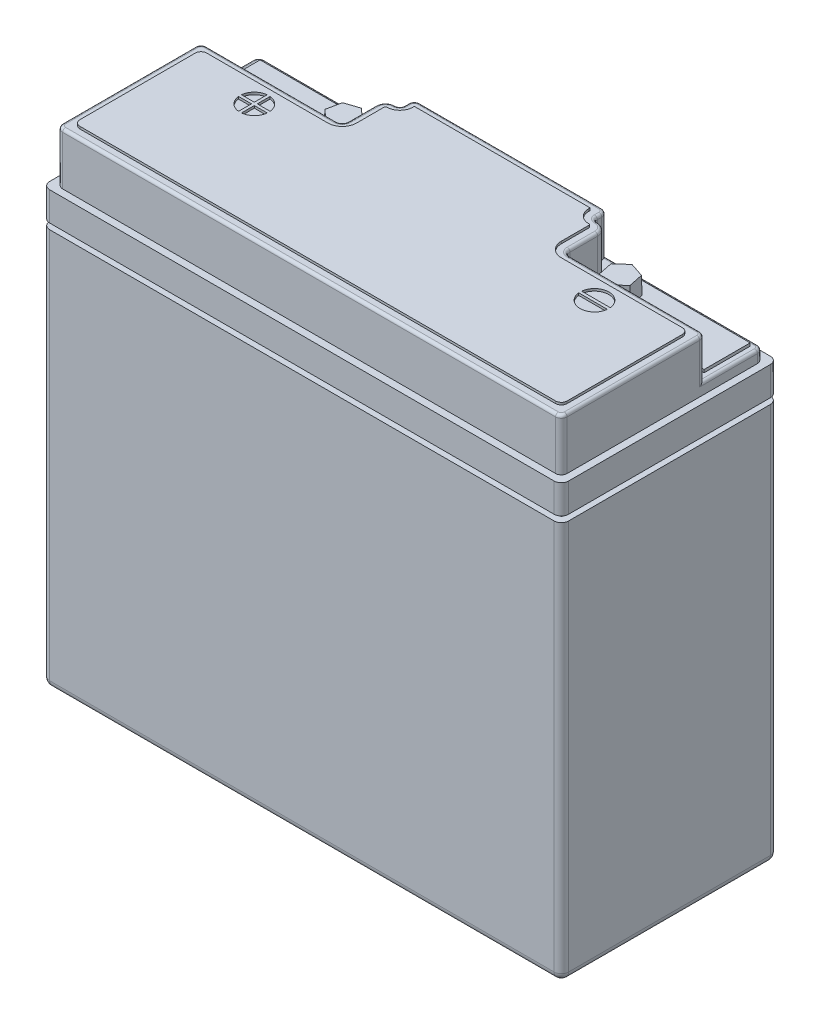
SolidWorks part; units mm, degrees
ref_plane "Front Plane" through (0, 0, 0) normal (0, 0, 1) x (1, 0, 0)
ref_plane "Top Plane" through (0, 0, 0) normal (0, 1, 0) x (1, 0, 0)
ref_plane "Right Plane" through (0, 0, 0) normal (1, 0, 0) x (0, 0, -1)
sketch "Sketch1" plane through (0, 0, 0) normal (0, 0, 1) x (1, 0, 0)
  line L1 (0, 0) -> (180, 0)
  line L2 (0, 0) -> (0, 150)
  line L3 (0, 150) -> (180, 150)
  line L4 (180, 0) -> (180, 150)
  dimension "D1" = 180
  dimension "D2" = 150
extrude "Battery Body" add sketch "Sketch1" against normal blind 75
fillet "Battery Body Fillet" radius 2.5 4 edges at (0, 0, -37.5) (90, 0, -75) (180, 0, -37.5) (90, 0, 0)
sketch "Sketch2" plane through (0, 150, 0) normal (0, 1, 0) x (-1, 0, 0)
  line L0 (-4.5, -2.5) -> (-175.5, -2.5)
  line L1 (-2.5, -70.5) -> (-2.5, -4.5)
  line L2 (-175.5, -72.5) -> (-4.5, -72.5)
  line L3 (-177.5, -4.5) -> (-177.5, -70.5)
  line L4 (-177.5, -75) -> (-2.5, -75) construction
  line L5 (-180, -72.5) -> (-180, -2.5) construction
  line L6 (-177.5, 0) -> (-2.5, 0) construction
  line L7 (0, -72.5) -> (0, -2.5) construction
  arc A0 (-177.5, -70.5) -> (-175.5, -72.5) centre (-175.5, -70.5) ccw
  arc A1 (-175.5, -2.5) -> (-177.5, -4.5) centre (-175.5, -4.5) ccw
  arc A2 (-2.5, -4.5) -> (-4.5, -2.5) centre (-4.5, -4.5) ccw
  arc A3 (-4.5, -72.5) -> (-2.5, -70.5) centre (-4.5, -70.5) ccw
  dimension "D3" = 2
  dimension "D4" = 2.5
  dimension "D5" = 2.5
  dimension "D1" = 2.5
  dimension "D2" = 2.5
extrude "Battery Top" add sketch "Sketch2" along normal blind 18
ref_plane "Plane1" through (0, 140, 0) normal (0, -1, 0) x (1, 0, 0)
sketch "Sketch3" plane through (0, 140, 0) normal (0, -1, 0) x (1, 0, 0)
  line L1 (2.5, -72.5) -> (177.5, -72.5)
  line L2 (2.5, -72.5) -> (2.5, -2.5)
  line L3 (2.5, -2.5) -> (177.5, -2.5)
  line L4 (177.5, -72.5) -> (177.5, -2.5)
  line L5 (0, -75) -> (180, -75)
  line L6 (180, -75) -> (180, 0)
  line L7 (0, 0) -> (180, 0)
  line L8 (0, -75) -> (0, 0)
  dimension "D1" = 2.5
extrude "Battery Body Grove" cut sketch "Sketch3" along normal blind 2
sketch "Sketch4" plane through (0, 168, 0) normal (0, 1, 0) x (-1, 0, 0)
  line L0 (-4.5, -52.5) -> (-49.5, -52.5)
  line L1 (-51.5, -54.5) -> (-51.5, -64.1)
  line L2 (-54.9, -67.5) -> (-55, -67.5)
  line L3 (-56.5, -69) -> (-56.5, -70.5)
  line L4 (-175.5, -72.5) -> (-4.5, -72.5)
  line L5 (-2.5, -70.5) -> (-2.5, -4.5)
  line L6 (-4.5, -2.5) -> (-175.5, -2.5)
  line L7 (-177.5, -4.5) -> (-177.5, -70.5)
  line L8 (-121.5, -72.5) -> (-58.5, -72.5)
  line L9 (-2.5, -50.5) -> (-2.5, -4.5)
  line L10 (-4.5, -2.5) -> (-175.5, -2.5)
  line L11 (-177.5, -4.5) -> (-177.5, -50.5)
  line L13 (-123.5, -69) -> (-123.5, -70.5)
  line L14 (-125.1, -67.5) -> (-125, -67.5)
  line L15 (-128.5, -54.5) -> (-128.5, -64.1)
  line L16 (-175.5, -52.5) -> (-130.5, -52.5)
  arc A0 (-49.5, -52.5) -> (-51.5, -54.5) centre (-49.5, -54.5) ccw
  arc A1 (-56.5, -69) -> (-55, -67.5) centre (-55, -69) cw
  arc A2 (-51.5, -64.1) -> (-54.9, -67.5) centre (-54.9, -64.1) cw
  arc A3 (-123.5, -69) -> (-125, -67.5) centre (-125, -69) ccw
  arc A4 (-177.5, -70.5) -> (-175.5, -72.5) centre (-175.5, -70.5) ccw
  arc A5 (-4.5, -72.5) -> (-2.5, -70.5) centre (-4.5, -70.5) ccw
  arc A6 (-2.5, -4.5) -> (-4.5, -2.5) centre (-4.5, -4.5) ccw
  arc A7 (-175.5, -2.5) -> (-177.5, -4.5) centre (-175.5, -4.5) ccw
  arc A8 (-121.5, -72.5) -> (-123.5, -70.5) centre (-121.5, -70.5) cw
  arc A9 (-56.5, -70.5) -> (-58.5, -72.5) centre (-58.5, -70.5) cw
  arc A10 (-2.5, -4.5) -> (-4.5, -2.5) centre (-4.5, -4.5) ccw
  arc A11 (-175.5, -2.5) -> (-177.5, -4.5) centre (-175.5, -4.5) ccw
  arc A12 (-128.5, -64.1) -> (-125.1, -67.5) centre (-125.1, -64.1) ccw
  arc A13 (-130.5, -52.5) -> (-128.5, -54.5) centre (-130.5, -54.5) cw
  arc A14 (-177.5, -50.5) -> (-175.5, -52.5) centre (-175.5, -50.5) ccw
  arc A15 (-2.5, -50.5) -> (-4.5, -52.5) centre (-4.5, -50.5) cw
  point P19 (-51.5, -52.5)
  point P24 (-51.5, -67.5)
  point P45 (-2.5, -52.5)
  dimension "D6" = 2
  dimension "D7" = 3.4
  dimension "D8" = 1.5
  dimension "D9" = 2
  dimension "D10" = 2
  dimension "D11" = 2
  dimension "D12" = 49
  dimension "D13" = 2
  dimension "D14" = 3.4
  dimension "D15" = 1.5
  dimension "D2" = 20
  dimension "D3" = 49
  dimension "D4" = 15
  dimension "D5" = 54
  dimension "D16" = 15
  dimension "D17" = 54
  dimension "D1" = 0
extrude "Terminal Cut-outs" cut sketch "Sketch4" against normal blind 14 flip side to cut
fillet "Top Fillet" radius 1 24 edges at (176.9142, 168, -3.0858) (177.5, 168, -27.5) (176.9142, 168, -51.9142) (153, 168, -52.5) (129.0858, 168, -53.0858) (128.5, 168, -59.3) (127.5042, 168, -66.5042) (125.05, 168, -67.5) (123.9393, 168, -67.9393) (123.5, 168, -69.75) (122.9142, 168, -71.9142) (90, 168, -72.5) (57.0858, 168, -71.9142) (56.5, 168, -69.75) (56.0607, 168, -67.9393) (54.95, 168, -67.5) (52.4958, 168, -66.5042) (51.5, 168, -59.3) (50.9142, 168, -53.0858) (27, 168, -52.5) (3.0858, 168, -51.9142) (2.5, 168, -27.5) (3.0858, 168, -3.0858) (90, 168, -2.5)
fillet "Terminal Fillet+" radius 1 3 edges at (31.5, 154, -72.5) (3.0858, 154, -71.9142) (2.5, 154, -60.5)
fillet "Terminal Fillet-" radius 1 3 edges at (148.5, 154, -72.5) (176.9142, 154, -71.9142) (177.5, 154, -60.5)
sketch "Sketch5" plane through (0, 154, 0) normal (0, 1, 0) x (-1, 0, 0)
  line L1 (-5, -70.5) -> (-50, -70.5)
  line L2 (-5, -70.5) -> (-5, -54.5)
  line L3 (-5, -54.5) -> (-50, -54.5)
  line L4 (-50, -70.5) -> (-50, -54.5)
  line L9 (-2.5, -50.5) -> (-2.5, -70.5) construction
  line L10 (-4.5, -72.5) -> (-58.5, -72.5) construction
  line L11 (-34, -62.5) -> (-50, -62.5) construction
  line L13 (-90, -71.5) -> (-90, -20.015) construction
  line L14 (-121.5, -71.5) -> (-58.5, -71.5) construction
  circle A0 centre (-42, -62.5) radius 4.5
  dimension "D7" = 9
  dimension "D8" = 8
  dimension "D2" = 45
  dimension "D4" = 2.5
  dimension "D5" = 2
  dimension "D6" = 16
extrude "Terminal Pad+" add sketch "Sketch5" along normal blind 1
sketch "Sketch6" plane through (0, 168, 0) normal (0, 1, 0) x (-1, 0, 0)
  line L0 (-30.5, -47.4749) -> (-30.5, -43)
  line L1 (-31.5, -47.4749) -> (-31.5, -43)
  line L2 (-30.5, -42) -> (-26.0251, -42)
  line L3 (-30.5, -43) -> (-26.0251, -43)
  line L4 (-30.5, -42) -> (-30.5, -37.5251)
  line L5 (-31.5, -42) -> (-31.5, -37.5251)
  line L12 (-36, -42.5) -> (-26, -42.5) construction
  line L13 (-31, -47.5) -> (-31, -37.5) construction
  line L14 (-35.9749, -43) -> (-31.5, -43)
  line L15 (-35.9749, -42) -> (-31.5, -42)
  line L16 (-90, -69.5) -> (-90, -28.7706) construction
  line L17 (-144, -42) -> (-154, -42)
  line L18 (-144, -43) -> (-154, -43)
  line L24 (-5.5, -5.5) -> (-174.5, -5.5)
  line L25 (-174.5, -5.5) -> (-174.5, -49.5)
  line L26 (-174.5, -49.5) -> (-130.5, -49.5)
  line L27 (-125.5, -54.5) -> (-125.5, -64.1)
  line L28 (-125.1, -64.5) -> (-125, -64.5)
  line L29 (-120.5, -69) -> (-120.5, -69.5)
  line L30 (-120.5, -69.5) -> (-59.5, -69.5)
  line L31 (-59.5, -69.5) -> (-59.5, -69)
  line L32 (-55, -64.5) -> (-54.9, -64.5)
  line L33 (-54.5, -64.1) -> (-54.5, -54.5)
  line L34 (-49.5, -49.5) -> (-5.5, -49.5)
  line L35 (-5.5, -49.5) -> (-5.5, -5.5)
  line L36 (-7.5, -5.5) -> (-172.5, -5.5)
  line L37 (-174.5, -7.5) -> (-174.5, -47.5)
  line L38 (-172.5, -49.5) -> (-130.5, -49.5)
  line L39 (-125.5, -54.5) -> (-125.5, -64.1)
  line L40 (-125.1, -64.5) -> (-125, -64.5)
  line L41 (-120.5, -69) -> (-120.5, -69.5)
  line L42 (-120.5, -69.5) -> (-59.5, -69.5)
  line L43 (-59.5, -69.5) -> (-59.5, -69)
  line L44 (-55, -64.5) -> (-54.9, -64.5)
  line L45 (-54.5, -64.1) -> (-54.5, -54.5)
  line L46 (-49.5, -49.5) -> (-7.5, -49.5)
  line L47 (-5.5, -47.5) -> (-5.5, -7.5)
  arc A0 (-144.0251, -43) -> (-153.9749, -43) centre (-149, -42.5) cw
  arc A1 (-30.5, -47.4749) -> (-26.0251, -43) centre (-31, -42.5) ccw
  arc A2 (-26.0251, -42) -> (-30.5, -37.5251) centre (-31, -42.5) ccw
  arc A3 (-31.5, -37.5251) -> (-35.9749, -42) centre (-31, -42.5) ccw
  arc A12 (-174.5, -47.5) -> (-172.5, -49.5) centre (-172.5, -47.5) ccw
  arc A13 (-172.5, -5.5) -> (-174.5, -7.5) centre (-172.5, -7.5) ccw
  arc A14 (-5.5, -7.5) -> (-7.5, -5.5) centre (-7.5, -7.5) ccw
  arc A15 (-7.5, -49.5) -> (-5.5, -47.5) centre (-7.5, -47.5) ccw
  arc A16 (-35.9749, -43) -> (-31.5, -47.4749) centre (-31, -42.5) ccw
  arc A17 (-153.9749, -42) -> (-144.0251, -42) centre (-149, -42.5) cw
  arc A24 (-125.5, -54.5) -> (-130.5, -49.5) centre (-130.5, -54.5) ccw
  arc A25 (-125.5, -64.1) -> (-125.1, -64.5) centre (-125.1, -64.1) ccw
  arc A26 (-120.5, -69) -> (-125, -64.5) centre (-125, -69) ccw
  arc A27 (-55, -64.5) -> (-59.5, -69) centre (-55, -69) ccw
  arc A28 (-54.9, -64.5) -> (-54.5, -64.1) centre (-54.9, -64.1) ccw
  arc A29 (-49.5, -49.5) -> (-54.5, -54.5) centre (-49.5, -54.5) ccw
  arc A30 (-125.5, -54.5) -> (-130.5, -49.5) centre (-130.5, -54.5) ccw
  arc A31 (-125.5, -64.1) -> (-125.1, -64.5) centre (-125.1, -64.1) ccw
  arc A32 (-120.5, -69) -> (-125, -64.5) centre (-125, -69) ccw
  arc A33 (-55, -64.5) -> (-59.5, -69) centre (-55, -69) ccw
  arc A34 (-54.9, -64.5) -> (-54.5, -64.1) centre (-54.9, -64.1) ccw
  arc A35 (-49.5, -49.5) -> (-54.5, -54.5) centre (-49.5, -54.5) ccw
  dimension "D2" = 2
  dimension "D3" = 10
  dimension "D6" = 7
  dimension "D7" = 25.5
  dimension "D1" = 2
  dimension "D4" = 0.5
  dimension "D5" = 0.5
  dimension "D8" = 0.5
  dimension "D9" = 0.5
extrude "Top terminal Marking" add sketch "Sketch6" along normal blind 0.8
sketch "Sketch7" plane through (0, 154, 0) normal (0, 1, 0) x (-1, 0, 0)
  line L4 (-177.5, -70.5) -> (-177.5, -50.5) construction
  line L5 (-121.5, -72.5) -> (-175.5, -72.5) construction
  line L10 (-175, -70.5) -> (-130, -70.5)
  line L11 (-175, -70.5) -> (-175, -54.5)
  line L12 (-175, -54.5) -> (-130, -54.5)
  line L13 (-130, -70.5) -> (-130, -54.5)
  circle A2 centre (-138, -62.5) radius 4.5
  dimension "D5" = 8
  dimension "D6" = 9
  dimension "D7" = 8
  dimension "D1" = 45
  dimension "D2" = 16
  dimension "D3" = 2.5
  dimension "D4" = 2
extrude "Terminal Pad-" add sketch "Sketch7" along normal blind 1
sketch "Sketch9" plane through (0, 155, 0) normal (0, 1, 0) x (-1, 0, 0)
  line L0 (-90, -72.5) -> (-90, -17.5664) construction
  line L1 (-36.9779, -60.8292) -> (-40.9359, -57.3154)
  line L2 (-40.9359, -57.3154) -> (-45.9579, -58.9862)
  line L3 (-45.9579, -58.9862) -> (-47.0221, -64.1708)
  line L4 (-47.0221, -64.1708) -> (-43.0641, -67.6846)
  line L5 (-43.0641, -67.6846) -> (-38.0421, -66.0138)
  line L6 (-38.0421, -66.0138) -> (-36.9779, -60.8292)
  line L7 (-58.5, -72.5) -> (-121.5, -72.5) construction
  line L8 (-141.9579, -66.0138) -> (-143.0221, -60.8292)
  line L9 (-136.9359, -67.6846) -> (-141.9579, -66.0138)
  line L10 (-132.9779, -64.1708) -> (-136.9359, -67.6846)
  line L11 (-134.0421, -58.9862) -> (-132.9779, -64.1708)
  line L12 (-139.0641, -57.3154) -> (-134.0421, -58.9862)
  line L13 (-143.0221, -60.8292) -> (-139.0641, -57.3154)
  circle A0 centre (-42, -62.5) radius 4.5836 construction
  circle A1 centre (-138, -62.5) radius 4.5836 construction
  dimension "D1" = 9.1672
extrude "Terminals" add sketch "Sketch9" along normal blind 6 draft 1
sketch "Yuasa-Text"
